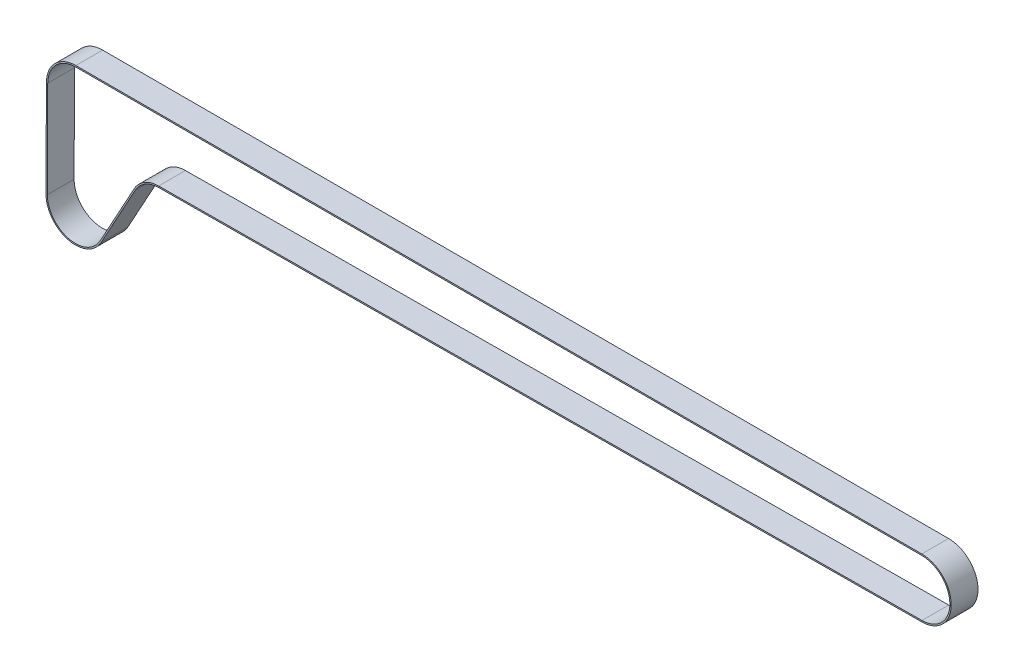
SolidWorks part; units mm, degrees
ref_plane "Front Plane" through (0, 0, 0) normal (0, 0, 1) x (1, 0, 0)
ref_plane "Top Plane" through (0, 0, 0) normal (0, 1, 0) x (1, 0, 0)
ref_plane "Right Plane" through (0, 0, 0) normal (1, 0, 0) x (0, 0, -1)
sketch "Sketch2" plane through (0, 0, 0) normal (0, 0, 1) x (1, 0, 0)
  line L0 (0, 0) -> (1, 0) construction
  line L1 (0, 0) -> (0, 1) construction
  line L2 (0, 10.5) -> (-316, 10.5)
  line L3 (-326.4999, 0.0436) -> (-326.6499, -36.1064)
  line L4 (-306.9415, -41.1952) -> (-294.2085, -17.9548)
  line L5 (-285.0737, -12.5003) -> (0.0737, -10.4997)
  arc A0 (0.0737, -10.4997) -> (0, 10.5) centre (0, 0) ccw
  arc A1 (-316, 10.5) -> (-326.4999, 0.0436) centre (-316, 0) ccw
  arc A2 (-326.6499, -36.1064) -> (-306.9415, -41.1952) centre (-316.15, -36.15) ccw
  arc A3 (-294.2085, -17.9548) -> (-285.0737, -12.5003) centre (-285, -23) cw
extrude "Extrude-Thin1" add sketch "Sketch2" along normal mid plane 10 from offset 2.5 thin offset against normal yes
